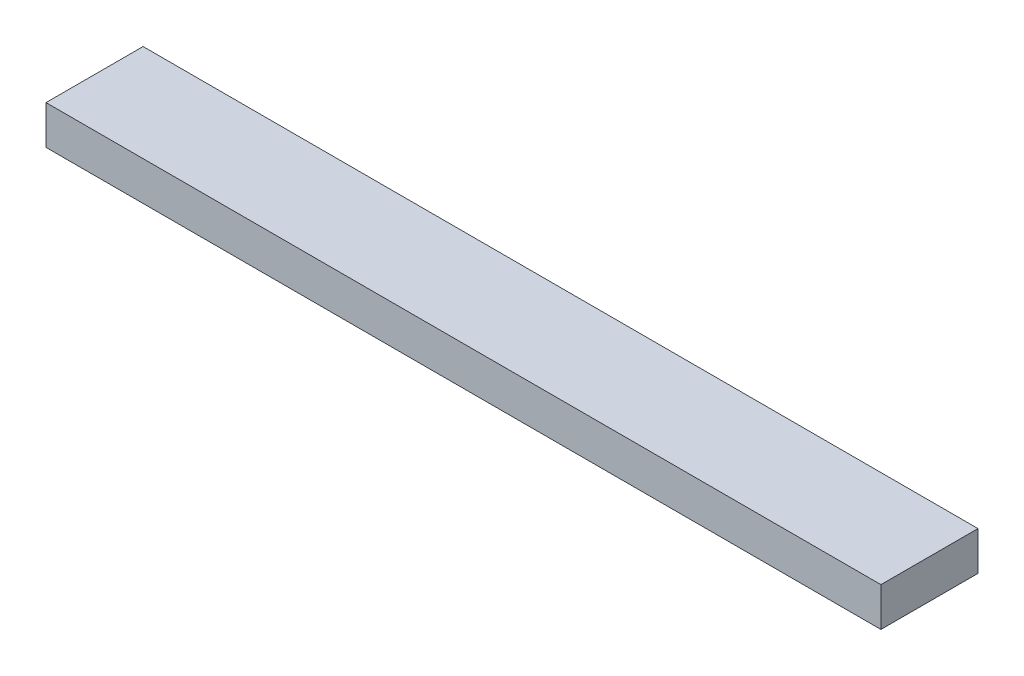
SolidWorks part; units mm, degrees
material "1023 Carbon Steel Sheet (SS)"
ref_plane "Front Plane" through (0, 0, 0) normal (0, 0, 1) x (1, 0, 0)
ref_plane "Top Plane" through (0, 0, 0) normal (0, 1, 0) x (1, 0, 0)
ref_plane "Right Plane" through (0, 0, 0) normal (1, 0, 0) x (0, 0, -1)
sketch "Sketch1" plane through (0, 0, 0) normal (1, 0, 0) x (0, 0, -1)
  line L1 (0, 0) -> (127, 0)
  line L2 (0, 0) -> (0, 50.8)
  line L3 (0, 50.8) -> (127, 50.8)
  line L4 (127, 0) -> (127, 50.8)
  dimension "D1" = 50.8
  dimension "D2" = 127
extrude "Boss-Extrude1" add sketch "Sketch1" along normal blind 1092.2
